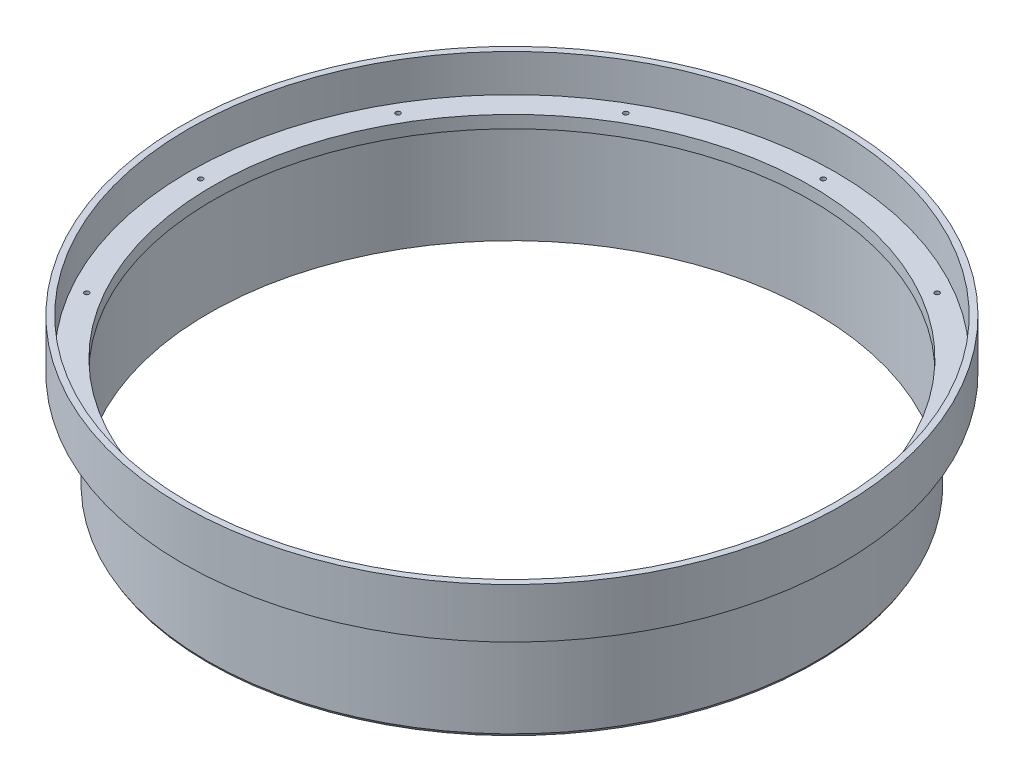
SolidWorks part; units mm, degrees
material "6061-T6 (SS)"
ref_plane "Front Plane" through (0, 0, 0) normal (0, 0, 1) x (1, 0, 0)
ref_plane "Top Plane" through (0, 0, 0) normal (0, 1, 0) x (1, 0, 0)
ref_plane "Right Plane" through (0, 0, 0) normal (1, 0, 0) x (0, 0, -1)
ref_axis "Axis1" through (0, 55, 0) along (0, -1, 0)
sketch "Cross Section" plane through (0, 0, 0) normal (0, 0, 1) x (1, 0, 0)
  line L0 (-76.2, 0) -> (-76.2, -3.175)
  line L1 (-76.2, -3.175) -> (-77.216, -3.175)
  line L2 (-77.216, -3.175) -> (-77.216, -28.575)
  line L3 (-77.216, -28.575) -> (-77.597, -27.9151)
  line L4 (0, 55) -> (0, -55) construction
  line L5 (-77.597, -27.9151) -> (-77.597, -3.175)
  line L6 (-77.597, -3.175) -> (-83.947, -3.175)
  line L7 (-83.947, -3.175) -> (-83.947, 9.525)
  line L8 (-83.947, 9.525) -> (-82.3595, 9.525)
  line L9 (-82.3595, 9.525) -> (-82.3595, 0)
  line L10 (-82.3595, 0) -> (-76.2, 0)
  line L11 (-76.2, 0) -> (0, 0) construction
  point P2 (0, 0)
  point P5 (-3.2425, 0.375)
  dimension "D1" = 1.016
  dimension "D2" = 25.4
  dimension "D3" = 0.381
  dimension "D4" = 30
  dimension "D5" = 6.35
  dimension "D6" = 12.7
  dimension "D7" = 1.5875
  dimension "D8" = 76.2
  dimension "D9" = 3.175
revolve "Main" add sketch "Cross Section" angle 360 about axis through (0, 55, 0) along (0, -1, 0)
sketch "Hole Location" plane through (0, 0, 0) normal (0, 1, 0) x (1, 0, 0)
  line L0 (0, 0) -> (-79.2797, 0) construction
  circle A0 centre (0, 0) radius 79.2797 construction
  dimension "D1" = 158.5595
hole_wizard "#0-80 Tapped Hole1" positions "Sketch5" profile "Sketch7" tap size "#0-80" standard "ANSI Inch"
sketch "Sketch5" plane through (0, 0, 0) normal (0, 1, 0) x (1, 0, 0)
  point P0 (-79.2797, 0)
sketch "Sketch7" plane through (-79.2797, 0, 0) normal (1, 0, 0) x (0, 0, 1)
  line L0 (0, 0) -> (0, 2.8979)
  line L1 (0, 2.8979) -> (0.5956, 2.54)
  line L2 (0.5956, 2.54) -> (0.5956, 0)
  line L5 (0.5956, 0) -> (0, 0)
  line L10 (0, 2.8979) -> (-0.5956, 2.54) construction
  line L11 (0, -6.35) -> (0, 107.95) construction
  dimension "Tap Drill Dia." = 1.1913
  dimension "Tap Drill Depth" = 2.54
  dimension "Drill Angle" = 118
cosmetic thread "Hole Thread1" parameters "D1"=2.54, "D2"=1.524
pattern_circular "Screw Holes" count 12 over 360 about axis through (0, 0, 0) along (0, 1, 0) of "#0-80 Tapped Hole1"
